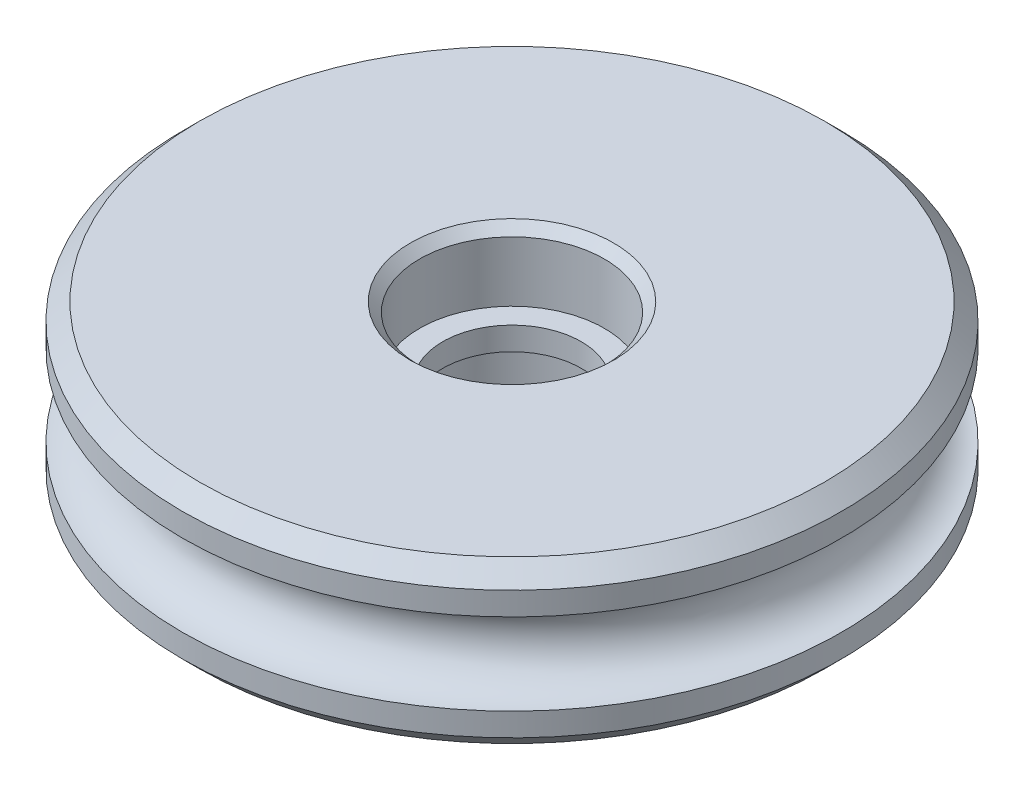
SolidWorks part; units mm, degrees
material "ABS"
ref_plane "Front Plane" through (0, 0, 0) normal (0, 0, 1) x (1, 0, 0)
ref_plane "Top Plane" through (0, 0, 0) normal (0, 1, 0) x (1, 0, 0)
ref_plane "Right Plane" through (0, 0, 0) normal (1, 0, 0) x (0, 0, -1)
sketch "Sketch1" plane through (0, 0, 0) normal (1, 0, 0) x (0, 0, -1)
  line L0 (0, 19.0174) -> (0, -19.7603) construction
  line L1 (-4, 3.5) -> (-13.5274, 3.5)
  line L3 (-14.2621, 0) -> (-12.4968, 0) construction
  line L4 (-12.4968, 0) -> (-3, 0)
  line L7 (-3, 0) -> (-3, 0.5)
  line L8 (-3, 0.5) -> (-4, 0.5)
  line L9 (-4, 0.5) -> (-4, 3.5)
  line L10 (-14.2621, 1.7653) -> (-14.2621, 2.7653)
  line L11 (-14.2621, 2.7653) -> (-13.5274, 3.5)
  arc A0 (-12.4968, 0) -> (-14.2621, 1.7653) centre (-14.2621, 0) ccw
  dimension "D1" = 3.5306
  dimension "D2" = 24.9936
  dimension "D3" = 3
  dimension "D4" = 0.5
  dimension "D5" = 1
  dimension "D6" = 8
  dimension "D7" = 1
  dimension "D8" = 45
revolve "Revolve1" add sketch "Sketch1" angle 360 about L0
mirror "Mirror1" about plane through (0, 0, 0) normal (0, 1, 0) of "Revolve1"
chamfer "Chamfer1" distance 0.4 angle 45 2 edges at (0, 3.5, 4) (0, -3.5, 4)
